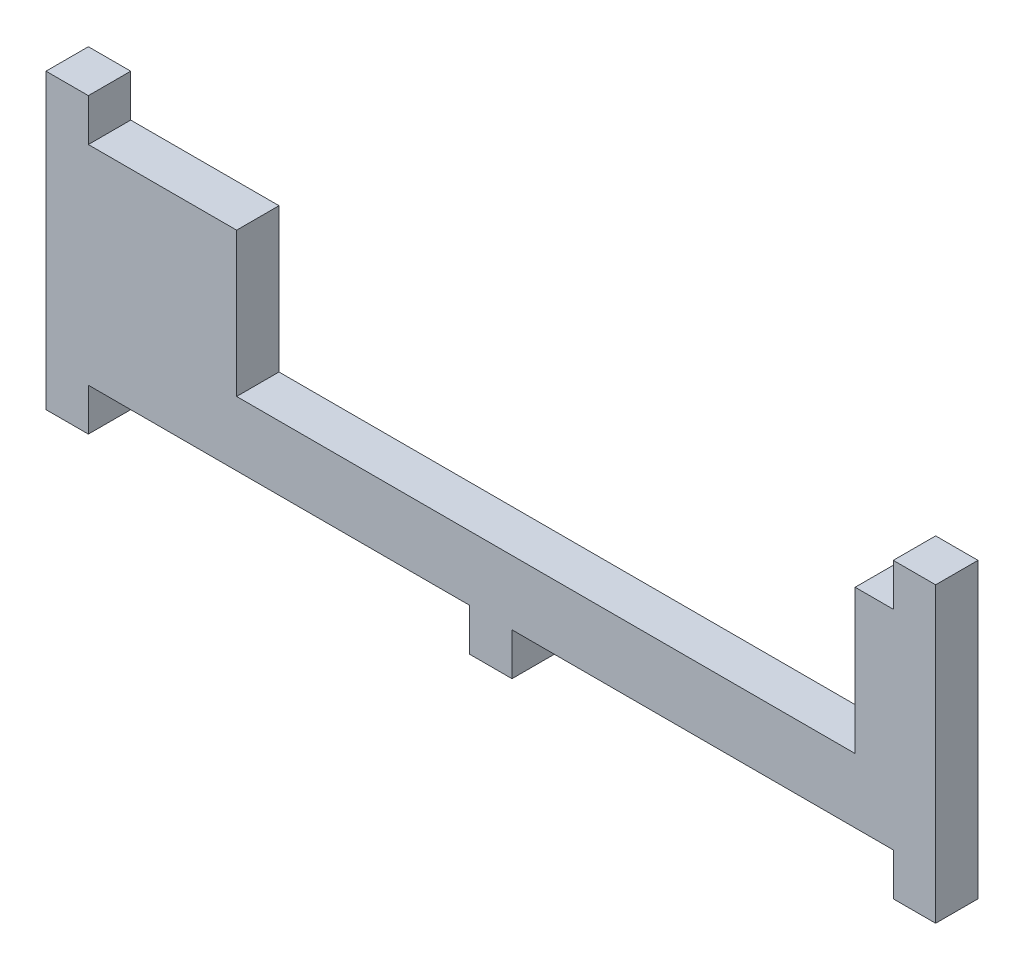
SolidWorks part; units mm, degrees
ref_plane "Front" through (0, 0, 0) normal (0, 0, 1) x (1, 0, 0)
ref_plane "Top" through (0, 0, 0) normal (0, 1, 0) x (1, 0, 0)
ref_plane "Right" through (0, 0, 0) normal (1, 0, 0) x (0, 0, -1)
sketch "Sketch1" plane through (0, 0, 0) normal (0, 0, 1) x (1, 0, 0)
  line L1 (-52.5, -6.15) -> (52.5, -6.15)
  line L2 (-52.5, -6.15) -> (-52.5, 6.15)
  line L3 (-52.5, 6.15) -> (52.5, 6.15)
  line L4 (52.5, -6.15) -> (52.5, 6.15)
  line L5 (-52.5, -6.15) -> (52.5, 6.15) construction
  line L6 (-52.5, 6.15) -> (52.5, -6.15) construction
  point P0 (0, 0)
  dimension "D1" = 12.3
  dimension "D2" = 105
extrude "Boss-Extrude1" add sketch "Sketch1" along normal blind 5
sketch "Sketch2" plane through (0, -6.15, 0) normal (0, -1, 0) x (1, 0, 0)
  line L0 (-52.5, 5) -> (52.5, 5) construction
  line L1 (-52.5, 5) -> (-47.5, 5)
  line L2 (-52.5, 5) -> (-52.5, 0)
  line L3 (-52.5, 0) -> (-47.5, 0)
  line L4 (-47.5, 5) -> (-47.5, 0)
  line L5 (-52.5, 0) -> (52.5, 0) construction
  line L7 (52.5, 5) -> (52.5, 0) construction
  line L11 (47.5, 5) -> (52.5, 5)
  line L12 (47.5, 5) -> (47.5, 0)
  line L13 (47.5, 0) -> (52.5, 0)
  line L14 (52.5, 5) -> (52.5, 0)
  dimension "D1" = 5
  dimension "D3" = 5
  dimension "D5" = 95
extrude "Boss-Extrude2" add sketch "Sketch2" along normal blind 5
mirror "Mirror1" about plane through (-52.5, 6.15, 5) normal (0, -1, 0) of bodies 102
sketch "Sketch3" plane through (0, 18.45, 0) normal (0, 1, 0) x (1, 0, 0)
  line L0 (-47.5, 0) -> (47.5, 0) construction
  line L1 (-30, 0) -> (43, 0)
  line L2 (-30, 0) -> (-30, -5)
  line L3 (-30, -5) -> (43, -5)
  line L4 (43, 0) -> (43, -5)
  line L5 (-47.5, -5) -> (47.5, -5) construction
  line L6 (-52.5, -5) -> (-52.5, 0) construction
  dimension "D1" = 73
  dimension "D2" = 22.5
extrude "Cut-Extrude1" cut sketch "Sketch3" against normal blind 17
sketch "Sketch4" plane through (0, -6.15, 0) normal (0, -1, 0) x (1, 0, 0)
  line L0 (-47.5, 5) -> (47.5, 5) construction
  line L1 (-2.5, 5) -> (2.5, 5)
  line L2 (-2.5, 5) -> (-2.5, 0)
  line L3 (-2.5, 0) -> (2.5, 0)
  line L4 (2.5, 5) -> (2.5, 0)
  line L5 (-47.5, 0) -> (47.5, 0) construction
  line L6 (-47.5, 0) -> (-47.5, 5) construction
  dimension "D1" = 5
  dimension "D2" = 45
extrude "Boss-Extrude3" add sketch "Sketch4" along normal blind 5
